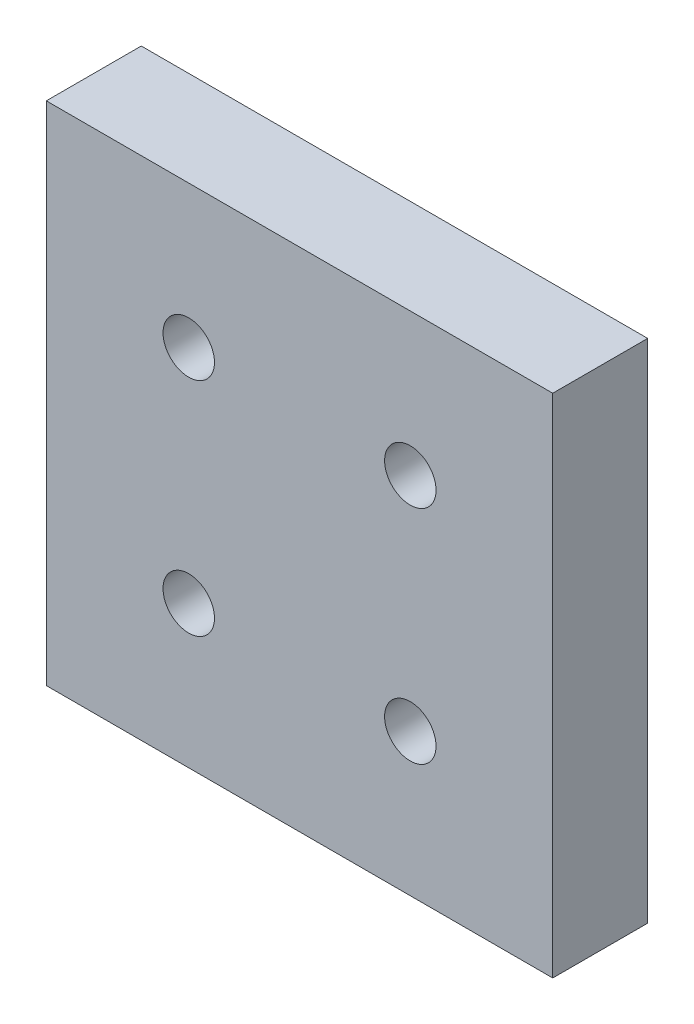
SolidWorks part; units mm, degrees
material "6061-T6 Al"
ref_plane "Front" through (0, 0, 0) normal (0, 0, 1) x (1, 0, 0)
ref_plane "Top" through (0, 0, 0) normal (0, 1, 0) x (1, 0, 0)
ref_plane "Right" through (0, 0, 0) normal (1, 0, 0) x (0, 0, -1)
sketch "Sketch1" plane through (0, 0, 0) normal (0, 0, 1) x (1, 0, 0)
  line L0 (0, 0) -> (0, 101.6) construction
  line L1 (-101.6, 101.6) -> (101.6, 101.6)
  line L2 (-101.6, 101.6) -> (-101.6, -101.6)
  line L3 (-101.6, -101.6) -> (101.6, -101.6)
  line L4 (101.6, 101.6) -> (101.6, -101.6)
  line L5 (0, 0) -> (-101.6, 0) construction
  dimension "D1" = 203.2
  dimension "D2" = 203.2
extrude "Boss-Extrude1" add sketch "Sketch1" along normal blind 38.1
hole_wizard "CBORE for 1/2 Socket Head Cap Screw1" positions "Sketch3" profile "Sketch4" counterbore size "1/2" standard "Ansi Inch" end condition through all
sketch "Sketch3" plane through (0, 0, 38.1) normal (0, 0, 1) x (1, 0, 0)
  line L0 (-44.45, 44.45) -> (44.45, 44.45) construction
  line L1 (-44.45, 44.45) -> (-44.45, -44.45) construction
  line L2 (-44.45, -44.45) -> (44.45, -44.45) construction
  line L3 (44.45, 44.45) -> (44.45, -44.45) construction
  line L4 (0, 0) -> (0, 44.45) construction
  line L5 (0, 0) -> (44.45, 0) construction
  point P0 (44.45, -44.45)
  point P1 (-44.45, -44.45)
  point P3 (-44.45, 44.45)
  point P5 (44.45, 44.45)
  dimension "D1" = 88.9
sketch "Sketch4" plane through (44.45, -44.45, 38.1) normal (1, 0, 0) x (0, -1, 0)
  line L0 (0, 0) -> (0, 38.1)
  line L1 (0, 38.1) -> (6.5481, 38.1)
  line L3 (6.5481, 38.1) -> (6.5481, 19.05)
  line L4 (6.5481, 19.05) -> (10.3187, 19.05)
  line L5 (10.3187, 19.05) -> (10.3187, 0)
  line L7 (10.3187, 0) -> (0, 0)
  line L11 (0, -6.35) -> (0, 107.95) construction
  dimension "Thru Hole Dia." = 13.0962
  dimension "Thru Hole Depth" = 38.1
  dimension "C'Bore Dia." = 20.6375
  dimension "C'Bore Depth" = 19.05
